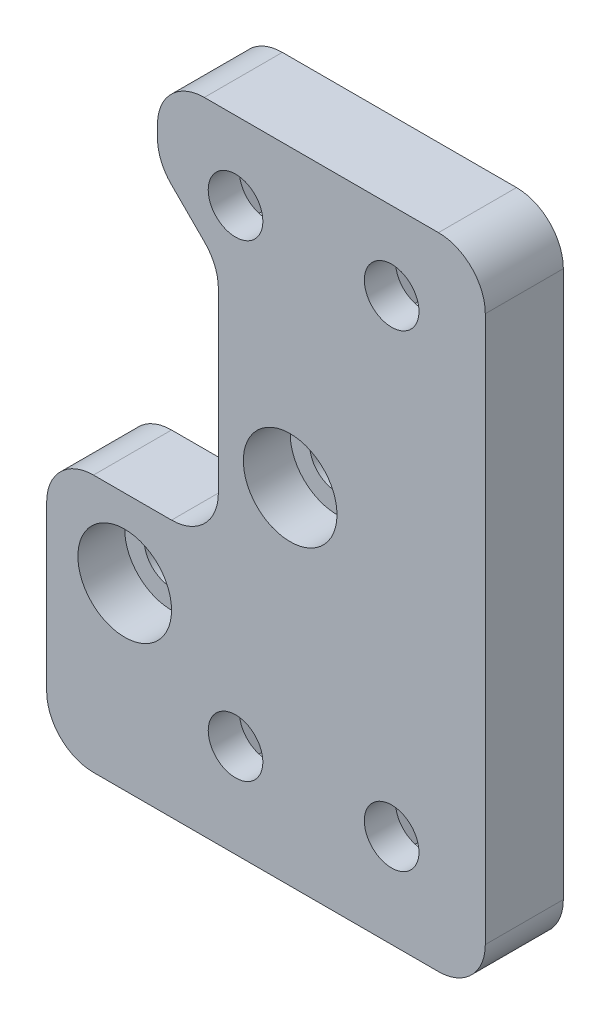
SolidWorks part; units mm, degrees
ref_plane "Front Plane" through (0, 0, 0) normal (0, 0, 1) x (1, 0, 0)
ref_plane "Top Plane" through (0, 0, 0) normal (0, 1, 0) x (1, 0, 0)
ref_plane "Right Plane" through (0, 0, 0) normal (1, 0, 0) x (0, 0, -1)
sketch "Sketch2" plane through (0, 0, 0) normal (0, 0, 1) x (1, 0, 0)
  line L1 (-32, 23.75) -> (32, 23.75) construction
  line L2 (-32, 23.75) -> (-32, -23.75) construction
  line L3 (-32, -23.75) -> (32, -23.75) construction
  line L4 (32, 23.75) -> (32, -23.75) construction
  line L5 (-32, 23.75) -> (32, -23.75) construction
  line L6 (-32, -23.75) -> (32, 23.75) construction
  line L7 (11, -21) -> (11, 20)
  line L8 (-17.1, -21) -> (11, -21)
  line L9 (-10, 20) -> (11, 20)
  line L10 (-5, 15) -> (5, 15) construction
  line L11 (-5, 15) -> (-5, -15) construction
  line L12 (-5, -15) -> (5, -15) construction
  line L13 (5, 15) -> (5, -15) construction
  line L14 (-5, 15) -> (5, -15) construction
  line L15 (-5, -15) -> (5, 15) construction
  line L16 (-17.1, -4.5) -> (-17.1, -21)
  line L19 (-6.1, -4.5) -> (-17.1, -4.5)
  line L20 (-12.5, 9) -> (-12.5, -9.5) construction
  line L21 (-12.5, 9) -> (-1.5, 9) construction
  line L22 (-10, 20) -> (-10, 15)
  line L23 (-10, 15) -> (-6.1, 11.1)
  line L24 (-6.1, 11.1) -> (-6.1, -4.5)
  circle A0 centre (-1.5, 1.1) radius 1.75
  circle A1 centre (-12.1, -9.5) radius 1.75
  circle A4 centre (-5, 15) radius 1.75
  circle A5 centre (-5, -15) radius 1.75
  circle A6 centre (5, 15) radius 1.75
  circle A7 centre (5, -15) radius 1.75
  circle A9 centre (-12.5, 9) radius 4.5 construction
  point P0 (0, 0)
  point P23 (0, 0)
  dimension "D1" = 30.5
  dimension "D2" = 3.5
  dimension "D5" = 3.5
  dimension "D6" = 64
  dimension "D7" = 47.5
  dimension "D8" = 14.25
  dimension "D13" = 6
  dimension "D17" = 9
  dimension "D3" = 10.6
  dimension "D4" = 10.6
  dimension "D9" = 6
  dimension "D10" = 10
  dimension "D11" = 30
  dimension "D12" = 5
  dimension "D14" = 5
  dimension "D15" = 5
  dimension "D16" = 5
  dimension "D18" = 18.5
  dimension "D19" = 11
  dimension "D20" = 45
  dimension "D21" = 5
  dimension "D22" = 11
extrude "Boss-Extrude1" add sketch "Sketch2" along normal blind 5
sketch "Sketch3" plane through (0, 0, 5) normal (0, 0, 1) x (1, 0, 0)
  circle A0 centre (-1.5, 1.1) radius 3
  circle A1 centre (-12.1, -9.5) radius 3
  dimension "D1" = 6
  dimension "D2" = 6
extrude "Cut-Extrude1" cut sketch "Sketch3" against normal blind 3
fillet "Fillet1" radius 3 8 edges at (11, 20, 2.5) (11, -21, 2.5) (-17.1, -21, 2.5) (-17.1, -4.5, 2.5) (-10, 15, 2.5) (-6.1, 11.1, 2.5) (-10, 20, 2.5) (-6.1, -4.5, 2.5)
sketch "Sketch4" plane through (0, 0, 0) normal (0, 0, -1) x (-1, 0, 0)
  line L1 (-3.3834, 12.2) -> (-1.7668, 15)
  line L2 (-1.7668, 15) -> (-3.3834, 17.8)
  line L3 (-3.3834, 17.8) -> (-6.6166, 17.8)
  line L4 (-6.6166, 17.8) -> (-8.2332, 15)
  line L5 (-8.2332, 15) -> (-6.6166, 12.2)
  line L6 (-6.6166, 12.2) -> (-3.3834, 12.2)
  line L7 (6.6166, 12.2) -> (8.2332, 15)
  line L8 (8.2332, 15) -> (6.6166, 17.8)
  line L9 (6.6166, 17.8) -> (3.3834, 17.8)
  line L10 (3.3834, 17.8) -> (1.7668, 15)
  line L11 (1.7668, 15) -> (3.3834, 12.2)
  line L12 (3.3834, 12.2) -> (6.6166, 12.2)
  line L13 (-3.3834, -17.8) -> (-1.7668, -15)
  line L14 (-1.7668, -15) -> (-3.3834, -12.2)
  line L15 (-3.3834, -12.2) -> (-6.6166, -12.2)
  line L16 (-6.6166, -12.2) -> (-8.2332, -15)
  line L17 (-8.2332, -15) -> (-6.6166, -17.8)
  line L18 (-6.6166, -17.8) -> (-3.3834, -17.8)
  line L19 (6.6166, -17.8) -> (8.2332, -15)
  line L20 (8.2332, -15) -> (6.6166, -12.2)
  line L21 (6.6166, -12.2) -> (3.3834, -12.2)
  line L22 (3.3834, -12.2) -> (1.7668, -15)
  line L23 (1.7668, -15) -> (3.3834, -17.8)
  line L24 (3.3834, -17.8) -> (6.6166, -17.8)
  circle A0 centre (-5, 15) radius 2.8 construction
  circle A1 centre (5, 15) radius 2.8 construction
  circle A2 centre (-5, -15) radius 2.8 construction
  circle A3 centre (5, -15) radius 2.8 construction
  dimension "D1" = 5.6
extrude "Cut-Extrude2" cut sketch "Sketch4" against normal blind 3
